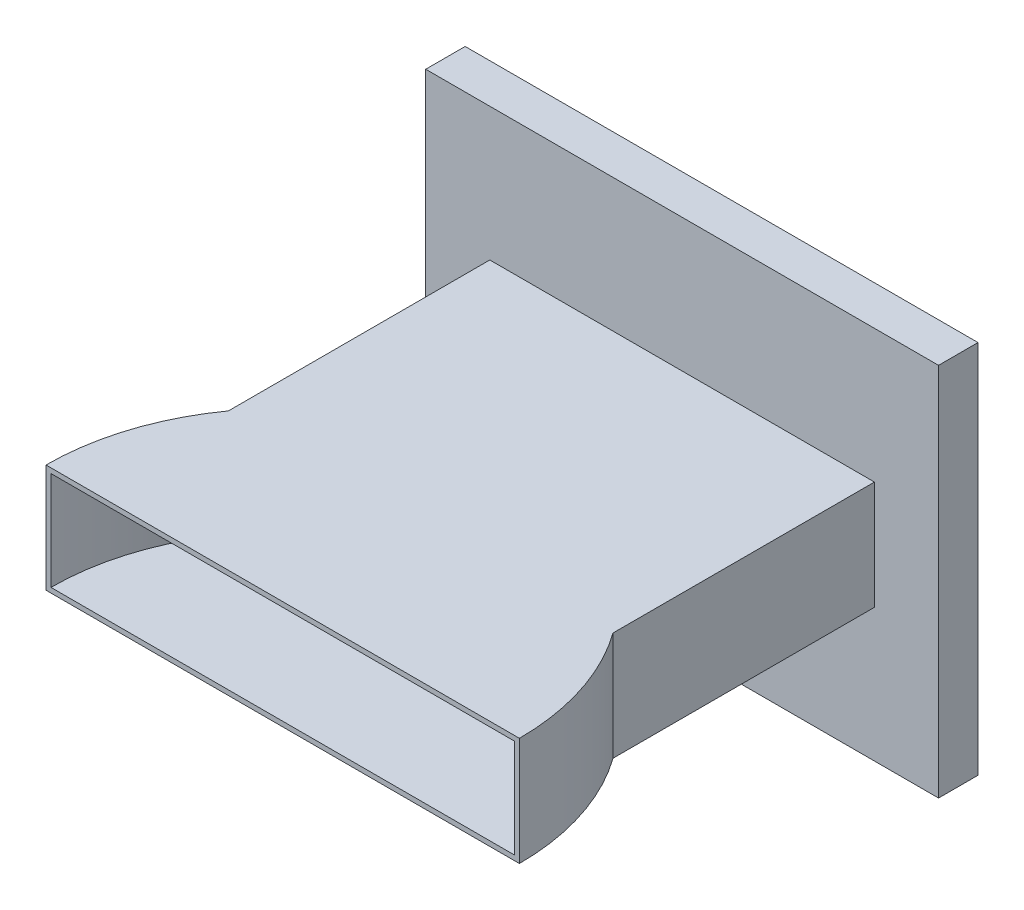
SolidWorks part; units mm, degrees
ref_plane "Front Plane" through (0, 0, 0) normal (0, 0, 1) x (1, 0, 0)
ref_plane "Top Plane" through (0, 0, 0) normal (0, 1, 0) x (1, 0, 0)
ref_plane "Right Plane" through (0, 0, 0) normal (1, 0, 0) x (0, 0, -1)
sketch "Sketch1" plane through (0, 0, 0) normal (0, 0, 1) x (1, 0, 0)
  line L0 (0, 0) -> (234, 0)
  line L5 (234, 0) -> (234, 66)
  line L6 (234, 66) -> (0, 66)
  line L7 (0, 66) -> (0, 0)
  line L8 (3, 3) -> (231, 3)
  line L9 (231, 3) -> (231, 63)
  line L10 (231, 63) -> (3, 63)
  line L11 (3, 63) -> (3, 3)
  point P0 (0, 0)
  dimension "D1" = 234
  dimension "D2" = 66
  dimension "D3" = 3
  dimension "D4" = 3
  dimension "D5" = 3
  dimension "D6" = 3
extrude "Boss-Extrude1" add sketch "Sketch1" along normal blind 243
sketch "Sketch2" plane through (0, 0, 0) normal (0, -1, 0) x (1, 0, 0)
  line L0 (0, 243) -> (234, 243) construction
  line L1 (-27, 243) -> (261, 243) construction
  line L2 (-27, 243) -> (261, 243)
  arc A0 (-27, 243) -> (261, 243) centre (117, 243) ccw
extrude "Boss-Extrude2" add sketch "Sketch2" against normal blind 66
sketch "Sketch3" plane through (0, 0, 243) normal (0, 0, 1) x (1, 0, 0)
  line L0 (261, 66) -> (-27, 66) construction
  line L1 (117, 63) -> (258, 63)
  line L2 (117, 63) -> (117, 3)
  line L3 (117, 3) -> (258, 3)
  line L4 (258, 63) -> (258, 3)
  line L5 (117, 63) -> (258, 3) construction
  line L6 (117, 3) -> (258, 63) construction
  line L7 (261, 66) -> (261, 0) construction
  point P0 (187.5, 33)
  point P5 (0, 0)
  point P8 (117, 66)
  point P11 (261, 33)
  dimension "D1" = 141
  dimension "D2" = 3
revolve "Cut-Revolve1" cut sketch "Sketch3" angle 360 about L2
sketch "Sketch4" plane through (0, 0, 0) normal (0, 1, 0) x (1, 0, 0)
  line L0 (0, 0) -> (234, 0) construction
  line L1 (-39, 0) -> (273, 0)
  line L2 (-39, 0) -> (-39, 24)
  line L3 (-39, 24) -> (273, 24)
  line L4 (273, 0) -> (273, 24)
  dimension "D1" = 312
  dimension "D2" = 24
  dimension "D3" = 39
extrude "Boss-Extrude3" add sketch "Sketch4" along normal blind 147 and the other way blind 81
